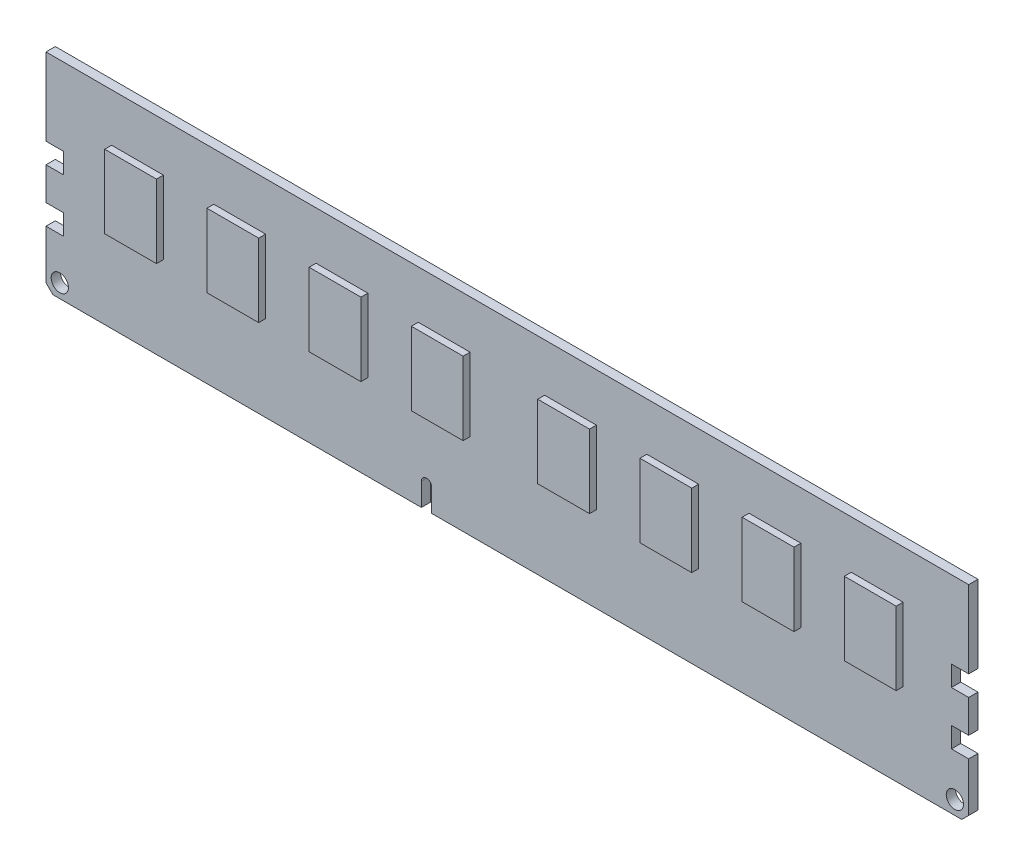
SolidWorks part; units mm, degrees
ref_plane "Front" through (0, 0, 0) normal (0, 0, 1) x (1, 0, 0)
ref_plane "Top" through (0, 0, 0) normal (0, 1, 0) x (1, 0, 0)
ref_plane "Right" through (0, 0, 0) normal (1, 0, 0) x (0, 0, -1)
sketch "Sketch1" plane through (0, 0, 0) normal (0, 0, 1) x (1, 0, 0)
  line L0 (-66.8, 18.75) -> (-64.3, 18.75)
  line L1 (0, 0) -> (-65.8, 0)
  line L2 (0, 0) -> (0, 29.95)
  line L3 (0, 29.95) -> (-66.8, 29.95)
  line L4 (-66.8, 1) -> (-66.8, 8.1)
  line L5 (-64.3, 18.75) -> (-64.3, 15.8)
  line L6 (-64.3, 15.8) -> (-66.8, 15.8)
  line L7 (-66.8, 11.05) -> (-64.3, 11.05)
  line L8 (-64.3, 11.05) -> (-64.3, 8.1)
  line L9 (-64.3, 8.1) -> (-66.8, 8.1)
  line L10 (-66.8, 11.05) -> (-66.8, 15.8)
  line L11 (-66.8, 18.75) -> (-66.8, 29.95)
  line L12 (-65.8, 0) -> (-66.8, 1)
  circle A0 centre (-64.8, 2) radius 1.25
  point P3 (-66.8, 0)
  dimension "D9" = 2.5
  dimension "D1" = 66.8
  dimension "D2" = 29.95
  dimension "D3" = 8.1
  dimension "D4" = 2.95
  dimension "D5" = 2.5
  dimension "D6" = 4.75
  dimension "D7" = 2
  dimension "D8" = 2
extrude "Boss-Extrude1" add sketch "Sketch1" along normal blind 0.675
sketch "Sketch2" plane through (0, 0, 0.675) normal (0, 0, 1) x (1, 0, 0)
  line L0 (-66.8, 29.95) -> (-66.8, 18.75) construction
  line L1 (-57.3, 23) -> (-49.8, 23)
  line L2 (-57.3, 23) -> (-57.3, 12.4)
  line L3 (-57.3, 12.4) -> (-49.8, 12.4)
  line L4 (-49.8, 23) -> (-49.8, 12.4)
  line L5 (0, 29.95) -> (-66.8, 29.95) construction
  line L6 (-42.5, 23) -> (-35, 23)
  line L7 (-42.5, 23) -> (-42.5, 12.4)
  line L8 (-42.5, 12.4) -> (-35, 12.4)
  line L9 (-35, 23) -> (-35, 12.4)
  line L10 (-27.7, 23) -> (-20.2, 23)
  line L11 (-27.7, 23) -> (-27.7, 12.4)
  line L12 (-27.7, 12.4) -> (-20.2, 12.4)
  line L13 (-20.2, 23) -> (-20.2, 12.4)
  line L14 (-12.9, 23) -> (-5.4, 23)
  line L15 (-12.9, 23) -> (-12.9, 12.4)
  line L16 (-12.9, 12.4) -> (-5.4, 12.4)
  line L17 (-5.4, 23) -> (-5.4, 12.4)
  dimension "D1" = 7.5
  dimension "D2" = 10.6
  dimension "D3" = 9.5
  dimension "D4" = 6.95
  dimension "D5" = 4
extrude "Boss-Extrude2" add sketch "Sketch2" along normal blind 1 contours L1 L4 L3 L2
mirror "Mirror1" about plane through (0, 0, 0) normal (0, 0, 1) of bodies 102
mirror "Mirror2" about plane through (0, 0, 0) normal (1, 0, 0) of bodies 103
sketch "Sketch3" plane through (0, 0, 0.675) normal (0, 0, 1) x (1, 0, 0)
  line L1 (-65.8, 0) -> (65.8, 0) construction
  line L3 (-12.45, 0) -> (-12.45, 3.3)
  line L6 (-10.95, 0) -> (-10.95, 3.3)
  line L7 (-11.7, 0) -> (-10.95, 3.3) construction
  line L8 (-12.45, 3.3) -> (-11.7, 0) construction
  line L9 (66.8, 8.1) -> (66.8, 1) construction
  line L10 (-12.45, 0) -> (-10.95, 0)
  arc A0 (-12.45, 3.3) -> (-10.95, 3.3) centre (-11.7, 3.3) cw
  point P0 (-11.7, 0)
  dimension "D1" = 78.5
  dimension "D2" = 0.75
  dimension "D3" = 0.75
  dimension "D4" = 3.3
extrude "Cut-Extrude1" cut sketch "Sketch3" against normal through all
